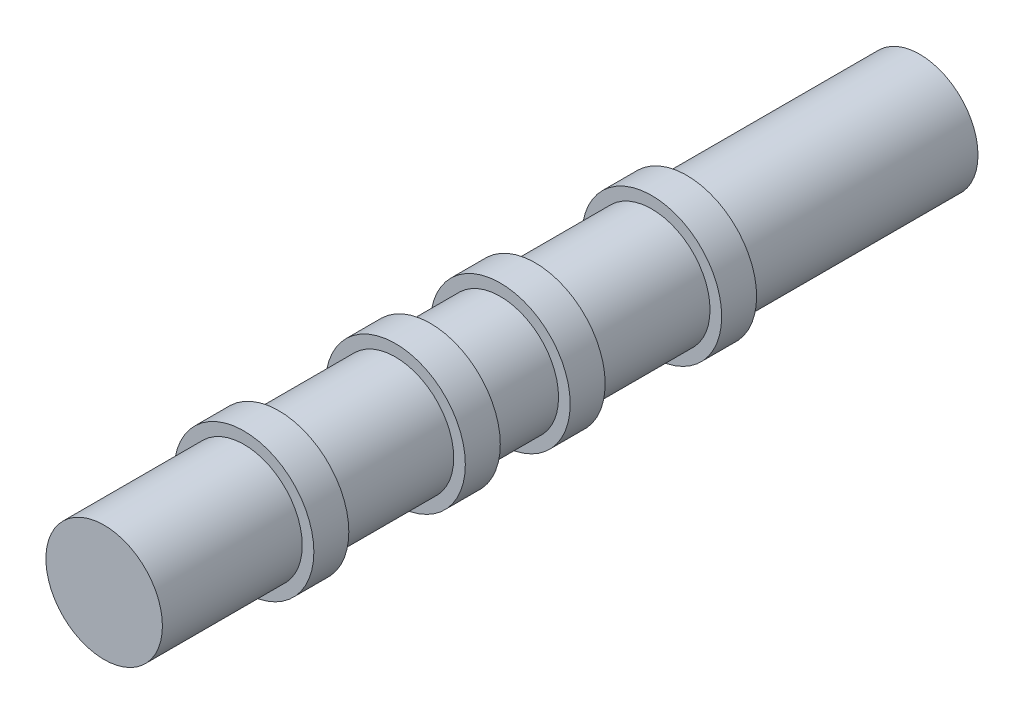
SolidWorks part; units mm, degrees
ref_plane "Front Plane" through (0, 0, 0) normal (0, 0, 1) x (1, 0, 0)
ref_plane "Top Plane" through (0, 0, 0) normal (0, 1, 0) x (1, 0, 0)
ref_plane "Right Plane" through (0, 0, 0) normal (1, 0, 0) x (0, 0, -1)
sketch "Sketch1" plane through (0, 0, 0) normal (0, 0, 1) x (1, 0, 0)
  circle A0 centre (0, 0) radius 5
  dimension "D1" = 10
extrude "Boss-Extrude1" add sketch "Sketch1" along normal blind 20 contours A0
sketch "Sketch2" plane through (0, 0, 20) normal (0, 0, 1) x (1, 0, 0)
  circle A0 centre (0, 0) radius 6
extrude "Boss-Extrude2" add sketch "Sketch2" along normal blind 3
sketch "Sketch3" plane through (0, 0, 23) normal (0, 0, 1) x (1, 0, 0)
  circle A0 centre (0, 0) radius 5
extrude "Boss-Extrude3" add sketch "Sketch3" along normal blind 10
sketch "Sketch4" plane through (0, 0, 33) normal (0, 0, 1) x (1, 0, 0)
  circle A0 centre (0, 0) radius 6
extrude "Boss-Extrude4" add sketch "Sketch4" along normal blind 3
sketch "Sketch5" plane through (0, 0, 36) normal (0, 0, 1) x (1, 0, 0)
  circle A0 centre (0, 0) radius 5
extrude "Boss-Extrude5" add sketch "Sketch5" along normal blind 6
sketch "Sketch6" plane through (0, 0, 42) normal (0, 0, 1) x (1, 0, 0)
  circle A0 centre (0, 0) radius 6
extrude "Boss-Extrude6" add sketch "Sketch6" along normal blind 3
sketch "Sketch7" plane through (0, 0, 45) normal (0, 0, 1) x (1, 0, 0)
  circle A0 centre (0, 0) radius 5
extrude "Boss-Extrude7" add sketch "Sketch7" along normal blind 10
sketch "Sketch8" plane through (0, 0, 55) normal (0, 0, 1) x (1, 0, 0)
  circle A0 centre (0, 0) radius 6
extrude "Boss-Extrude8" add sketch "Sketch8" along normal blind 3
sketch "Sketch9" plane through (0, 0, 58) normal (0, 0, 1) x (1, 0, 0)
  circle A0 centre (0, 0) radius 5
extrude "Boss-Extrude9" add sketch "Sketch9" along normal blind 12
